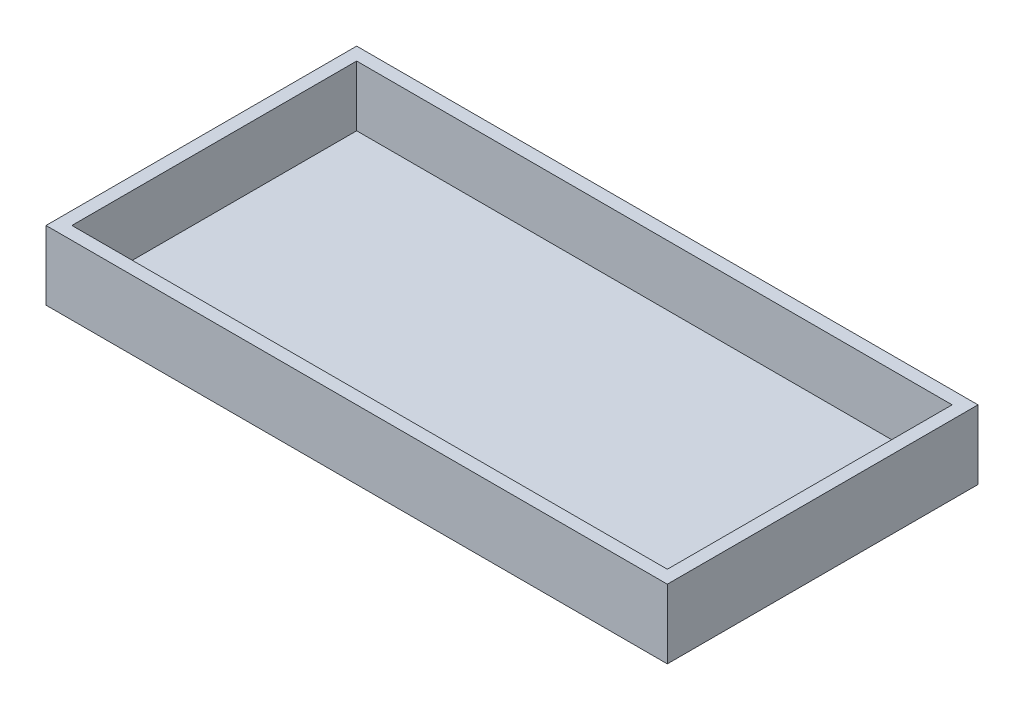
SolidWorks part; units mm, degrees
ref_plane "Front Plane" through (0, 0, 0) normal (0, 0, 1) x (1, 0, 0)
ref_plane "Top Plane" through (0, 0, 0) normal (0, 1, 0) x (1, 0, 0)
ref_plane "Right Plane" through (0, 0, 0) normal (1, 0, 0) x (0, 0, -1)
sketch "Sketch2" plane through (0, 0, 0) normal (0, 1, 0) x (1, 0, 0)
  line L1 (0, 457.2) -> (914.4, 457.2)
  line L2 (0, 457.2) -> (0, 0)
  line L3 (0, 0) -> (914.4, 0)
  line L4 (914.4, 457.2) -> (914.4, 0)
extrude "Boss-Extrude2" add sketch "Sketch2" against normal blind 12.7
sketch "Sketch1" plane through (0, 0, 0) normal (0, 1, 0) x (1, 0, 0)
  line L0 (19.05, 438.15) -> (895.35, 438.15)
  line L1 (0, 0) -> (914.4, 0)
  line L2 (0, 0) -> (0, 457.2)
  line L3 (0, 457.2) -> (914.4, 457.2)
  line L4 (914.4, 0) -> (914.4, 457.2)
  line L5 (0, 0) -> (914.4, 457.2) construction
  line L6 (0, 457.2) -> (914.4, 0) construction
  line L7 (895.35, 19.05) -> (895.35, 438.15)
  line L8 (19.05, 19.05) -> (895.35, 19.05)
  line L9 (19.05, 19.05) -> (19.05, 438.15)
  point P0 (0, 0)
  dimension "D1" = 914.4
  dimension "D2" = 457.2
  dimension "D3" = 19.05
extrude "Boss-Extrude3" add sketch "Sketch1" along normal blind 88.9
sketch "Sketch6" plane through (0, 0, 0) normal (0, 1, 0) x (1, 0, 0)
  line L0 (19.05, 228.6) -> (895.35, 228.6) construction
  line L1 (914.4, 457.2) -> (0, 457.2) construction
  line L4 (76.2, 457.2) -> (76.2, 0)
  line L5 (76.2, 457.2) -> (76.2, 0) construction
  line L6 (457.2, 19.05) -> (457.2, 438.15) construction
  line L7 (0, 457.2) -> (0, 0) construction
  circle A0 centre (76.2, 228.6) radius 25.4 construction
  circle A1 centre (838.2, 228.6) radius 25.4 construction
  dimension "D4" = 50.8
  dimension "D1" = 228.6
  dimension "D3" = 457.2
  dimension "D2" = 76.2
